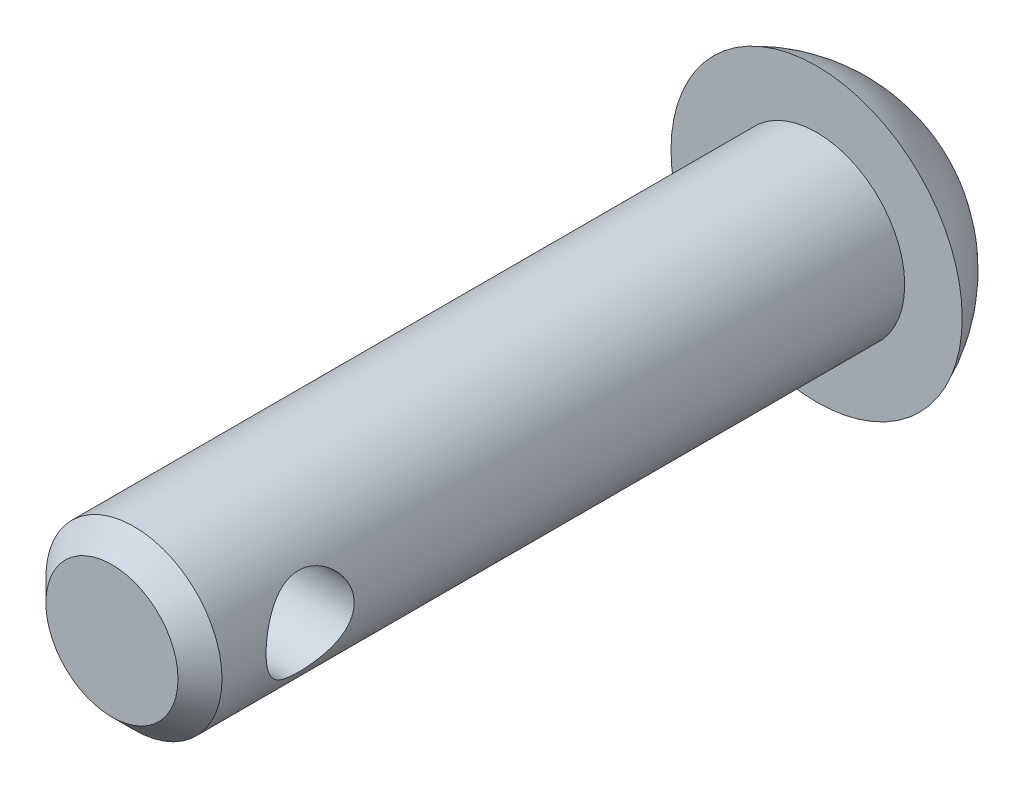
SolidWorks part; units mm, degrees
ref_plane "Front Plane" through (0, 0, 0) normal (0, 0, 1) x (1, 0, 0)
ref_plane "Top Plane" through (0, 0, 0) normal (0, 1, 0) x (1, 0, 0)
ref_plane "Right Plane" through (0, 0, 0) normal (1, 0, 0) x (0, 0, -1)
sketch "Sketch1" plane through (0, 0, 0) normal (0, 0, 1) x (1, 0, 0)
  circle A0 centre (0, 0) radius 2
  dimension "D1" = 4
extrude "Boss-Extrude1" add sketch "Sketch1" against normal blind 16
chamfer "Chamfer1" distance 0.5 angle 45 1 edges at (2, 0, 0)
sketch "Sketch4" plane through (0, 0, 0) normal (1, 0, 0) x (0, 0, -1)
  line L0 (13.2978, 0) -> (18.4171, 0) construction
  line L1 (16, 0) -> (16, 3.3059)
  line L2 (16, -2) -> (16, 2) construction
  line L3 (16, 0) -> (18.1749, 0)
  arc A0 (16, 3.3059) -> (18.1749, 0) centre (14.5749, 0) cw
  point P9 (0, 0)
  dimension "D2" = 3.6
  dimension "D1" = 3.3059
revolve "Revolve1" add sketch "Sketch4" angle 360 about L0
sketch "Sketch7" plane through (0, 0, 0) normal (1, 0, 0) x (0, 0, -1)
  circle A0 centre (2.5, 0) radius 1
  point P2 (0, 0)
  dimension "D2" = 2
  dimension "D1" = 13.5
extrude "Cut-Extrude1" cut sketch "Sketch7" against normal through all and the other way through all
